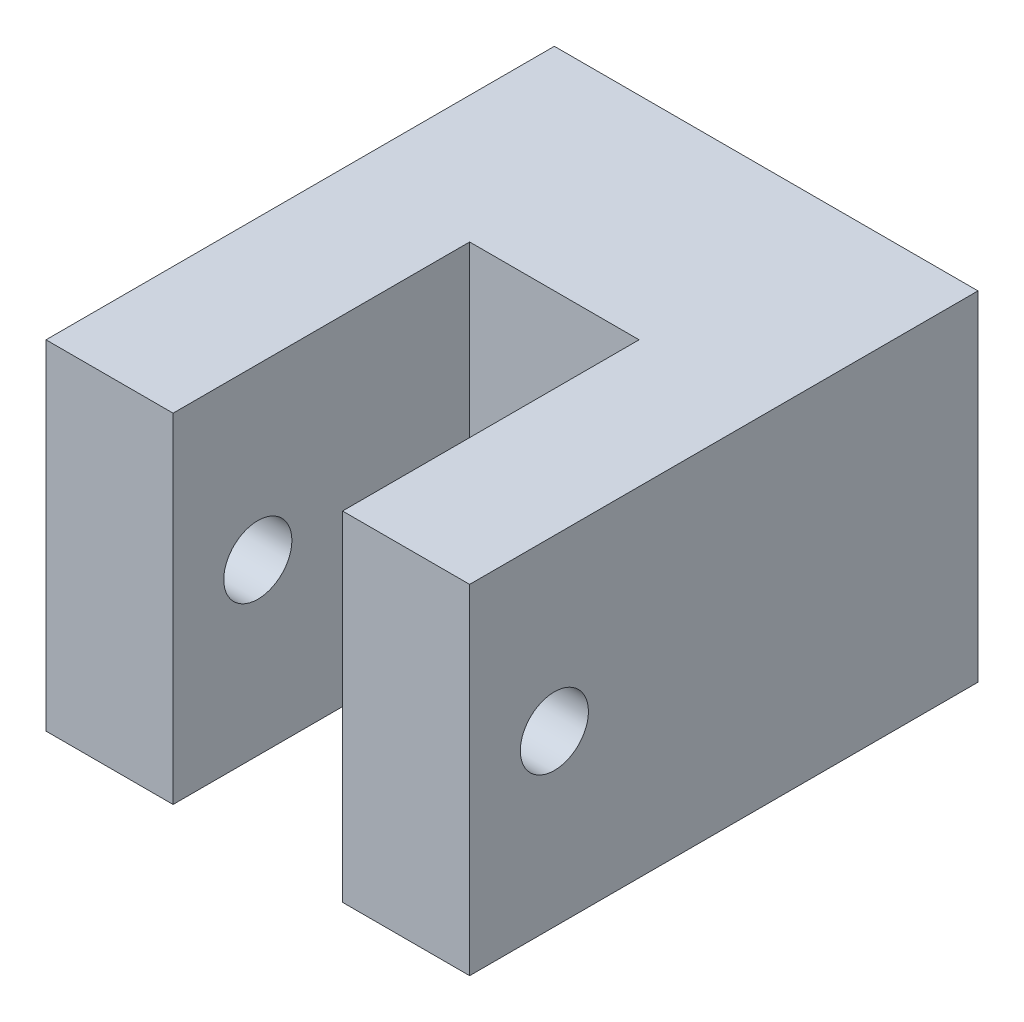
SolidWorks part; units mm, degrees
material "Delrin 2700 NC010, Low Viscosity Acetal Copolymer (SS)"
ref_plane "Front" through (0, 0, 0) normal (0, 0, 1) x (1, 0, 0)
ref_plane "Top" through (0, 0, 0) normal (0, 1, 0) x (1, 0, 0)
ref_plane "Right" through (0, 0, 0) normal (1, 0, 0) x (0, 0, -1)
sketch "Sketch1" plane through (0, 0, 0) normal (0, 0, 1) x (1, 0, 0)
  line L1 (0, 0) -> (31.75, 0)
  line L2 (0, 0) -> (0, 25.4)
  line L3 (0, 25.4) -> (31.75, 25.4)
  line L4 (31.75, 0) -> (31.75, 25.4)
  dimension "D1" = 25.4
  dimension "D2" = 31.75
extrude "Boss-Extrude1" add sketch "Sketch1" along normal blind 38.1
sketch "Sketch4" plane through (0, 0, 0) normal (0, 0, -1) x (-1, 0, 0)
  line L0 (0, 0) -> (-6.35, 12.7) construction
  line L3 (-31.75, 25.4) -> (-25.4, 12.7) construction
  point P0 (-25.4, 12.7)
  point P2 (-6.35, 12.7)
  dimension "D1" = 19.05
hole_wizard "1/4 (0.25) Diameter Hole1" positions "Sketch4" profile "Sketch3" hole size "1/4" standard "ANSI Inch"
sketch "Sketch3" plane through (25.4, 12.7, 0) normal (1, 0, 0) x (0, 1, 0)
  line L0 (0, 0) -> (0, 14.6077)
  line L1 (0, 14.6077) -> (3.175, 12.7)
  line L2 (3.175, 12.7) -> (3.175, 0)
  line L5 (3.175, 0) -> (0, 0)
  line L10 (0, 14.6077) -> (-3.175, 12.7) construction
  line L11 (0, -6.35) -> (0, 107.95) construction
  dimension "Hole Dia." = 6.35
  dimension "Hole Depth" = 12.7
  dimension "Drill Angle" = 118
sketch "Sketch5" plane through (0, 25.4, 0) normal (0, 1, 0) x (1, 0, 0)
  line L0 (31.75, -38.1) -> (0, -38.1) construction
  line L1 (9.525, -38.1) -> (22.225, -38.1)
  line L2 (9.525, -38.1) -> (9.525, -15.875)
  line L3 (9.525, -15.875) -> (22.225, -15.875)
  line L4 (22.225, -38.1) -> (22.225, -15.875)
  line L5 (0, 0) -> (9.525, -15.875) construction
  line L6 (31.75, 0) -> (22.225, -15.875) construction
  dimension "D1" = 12.7
  dimension "D2" = 22.225
extrude "Cut-Extrude2" cut sketch "Sketch5" against normal through all
sketch "Sketch8" plane through (31.75, 0, 0) normal (1, 0, 0) x (0, 0, -1)
  line L0 (-15.875, 0) -> (-15.875, 25.4) construction
  line L1 (-31.75, 25.4) -> (-31.75, 0) construction
  line L2 (-38.1, 25.4) -> (0, 25.4) construction
  line L3 (-38.1, 0) -> (0, 0) construction
  circle A0 centre (-31.75, 12.7) radius 12.7 construction
  point P0 (-31.75, 12.7)
  point P15 (0, 0)
  dimension "D1" = 25.4
  dimension "D2" = 15.875
hole_wizard "#10 Clearance Hole1" positions "Sketch8" profile "Sketch7" hole size "#10" standard "ANSI Inch" end condition through all
sketch "Sketch7" plane through (31.75, 12.7, 31.75) normal (0, 1, 0) x (0, 0, -1)
  line L0 (0, 0) -> (0, 31.75)
  line L1 (0, 31.75) -> (2.5527, 31.75)
  line L2 (2.5527, 31.75) -> (2.5527, 0)
  line L5 (2.5527, 0) -> (0, 0)
  line L11 (0, -6.35) -> (0, 107.95) construction
  dimension "Thru Hole Dia." = 5.1054
  dimension "Thru Hole Depth" = 31.75
